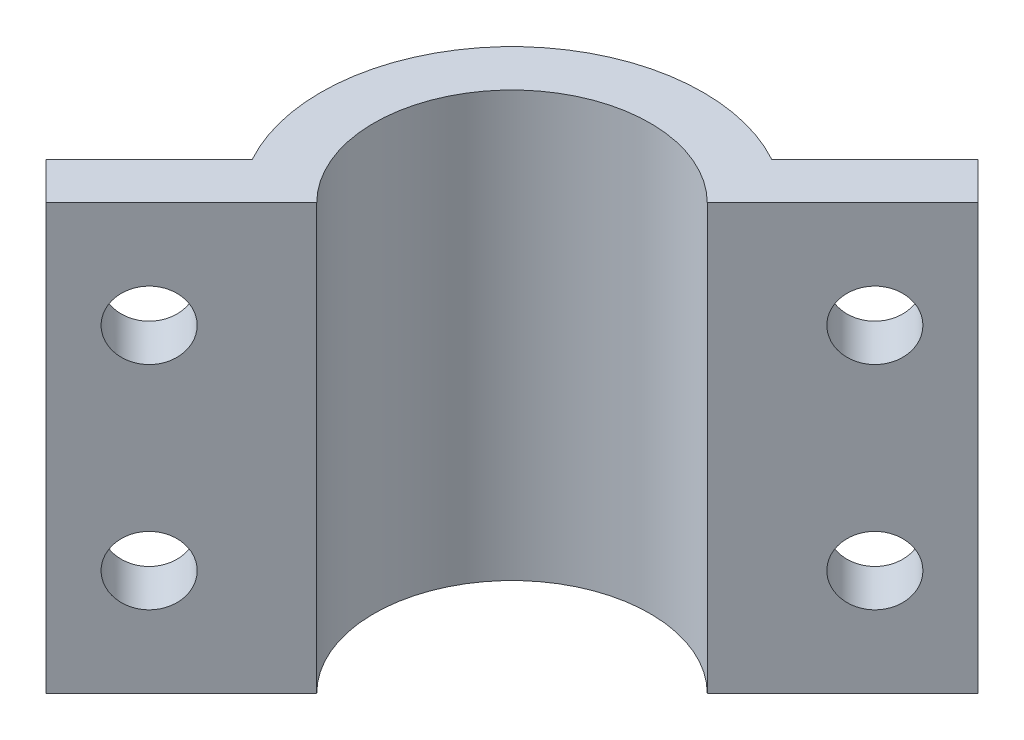
SolidWorks part; units mm, degrees
material "PLA"
ref_plane "Front Plane" through (0, 0, 0) normal (0, 0, 1) x (1, 0, 0)
ref_plane "Top Plane" through (0, 0, 0) normal (0, 1, 0) x (1, 0, 0)
ref_plane "Right Plane" through (0, 0, 0) normal (1, 0, 0) x (0, 0, -1)
sketch "Sketch1" plane through (0, 0, 0) normal (0, 1, 0) x (1, 0, 0)
  line L0 (0, 90) -> (0, -90) construction
  line L1 (-90, 0) -> (90, 0) construction
  line L2 (50, 10) -> (84, 10)
  line L3 (4, 90) -> (-4, 90)
  line L4 (10, 84) -> (10, 50)
  line L5 (4, -90) -> (-4, -90)
  line L6 (-10, 84) -> (-10, 50)
  line L7 (-84, 10) -> (-50, 10)
  line L8 (-90, 4) -> (-90, -4)
  line L9 (-84, -10) -> (-50, -10)
  line L10 (90, 4) -> (90, -4)
  line L11 (10, -50) -> (10, -84)
  line L12 (50, -10) -> (84, -10)
  line L13 (-10, -50) -> (-10, -84)
  arc A0 (4, 90) -> (10, 84) centre (4, 84) cw
  arc A1 (-4, 90) -> (-10, 84) centre (-4, 84) ccw
  arc A2 (84, 10) -> (90, 4) centre (84, 4) cw
  arc A3 (84, -10) -> (90, -4) centre (84, -4) ccw
  arc A4 (10, -84) -> (4, -90) centre (4, -84) cw
  arc A5 (-4, -90) -> (-10, -84) centre (-4, -84) cw
  arc A6 (-90, -4) -> (-84, -10) centre (-84, -4) ccw
  arc A7 (-84, 10) -> (-90, 4) centre (-84, 4) ccw
  arc A8 (50, 10) -> (10, 50) centre (50, 50) cw
  arc A9 (10, -50) -> (50, -10) centre (50, -50) cw
  arc A10 (-50, -10) -> (-10, -50) centre (-50, -50) cw
  arc A11 (-10, 50) -> (-50, 10) centre (-50, 50) cw
  point P5 (0, 0)
  point P8 (0, 0)
  point P16 (0, 90)
  point P23 (10, 90)
  point P26 (-10, 90)
  point P43 (10, -10)
  point P46 (-10, -10)
  dimension "D1" = 20
  dimension "D3" = 6
  dimension "D4" = 40
  dimension "D2" = 180
extrude "Boss-Extrude1" add sketch "Sketch1" along normal mid plane 3
hole_wizard "M3 Clearance Hole1" positions "Sketch3" profile "Sketch4" hole size "M3" standard "ANSI Metric" end condition up to next
sketch "Sketch3" plane through (0, 1.5, 0) normal (0, 1, 0) x (1, 0, 0)
  line L2 (-84, 4) -> (-39, 4) construction
  line L3 (-84, 4) -> (-84, -4) construction
  line L4 (-84, -4) -> (-39, -4) construction
  line L5 (-39, 4) -> (-39, -4) construction
  line L7 (-4, 84) -> (4, 84) construction
  line L8 (-4, 84) -> (-4, 39) construction
  line L9 (-4, 39) -> (4, 39) construction
  line L10 (4, 84) -> (4, 39) construction
  line L12 (39, 4) -> (84, 4) construction
  line L13 (39, 4) -> (39, -4) construction
  line L14 (39, -4) -> (84, -4) construction
  line L15 (84, 4) -> (84, -4) construction
  line L17 (-4, -39) -> (4, -39) construction
  line L18 (-4, -39) -> (-4, -84) construction
  line L19 (-4, -84) -> (4, -84) construction
  line L20 (4, -39) -> (4, -84) construction
  point P0 (-84, 4)
  point P3 (-84, -4)
  point P6 (-4, 84)
  point P9 (4, 84)
  point P12 (84, 4)
  point P15 (84, -4)
  point P18 (4, -84)
  point P21 (-4, -84)
  point P24 (-39, 4)
  point P26 (-39, -4)
  point P28 (39, 4)
  point P30 (39, -4)
  point P32 (4, -39)
  point P34 (-4, -39)
  point P36 (-4, 39)
  point P38 (4, 39)
  dimension "D1" = 45
sketch "Sketch4" plane through (-84, 1.5, -4) normal (1, 0, 0) x (0, 0, 1)
  line L0 (0, 0) -> (0, 3)
  line L1 (0, 3) -> (1.6, 3)
  line L2 (1.6, 3) -> (1.6, 0)
  line L5 (1.6, 0) -> (0, 0)
  line L11 (0, -6.35) -> (0, 107.95) construction
  dimension "Thru Hole Dia." = 3.2
  dimension "Thru Hole Depth" = 3
sketch "Sketch5" plane through (0, 1.5, 0) normal (0, 1, 0) x (1, 0, 0)
  circle A0 centre (0, 0) radius 15
  dimension "D1" = 30
extrude "Cut-Extrude1" cut sketch "Sketch5" against normal through all both and the other way through all
sketch "Sketch6" plane through (0, -1.5, 0) normal (0, -1, 0) x (1, 0, 0)
  line L0 (-21.7157, 21.7157) -> (21.7157, -21.7157) construction
  line L1 (-15.7626, 8.6915) -> (-25.4731, 18.402)
  line L2 (-25.4731, 18.402) -> (-18.402, 25.4731)
  line L3 (-18.402, 25.4731) -> (-8.6915, 15.7626)
  line L4 (8.6915, -15.7626) -> (18.402, -25.4731)
  line L5 (18.402, -25.4731) -> (25.4731, -18.402)
  line L6 (25.4731, -18.402) -> (15.7626, -8.6915)
  circle A0 centre (0, 0) radius 13
  arc A1 (-15.7626, 8.6915) -> (8.6915, -15.7626) centre (0, 0) ccw
  arc A2 (-50, 10) -> (-10, 50) centre (-50, 50) ccw construction
  arc A3 (50, -10) -> (10, -50) centre (50, -50) ccw construction
  circle A4 centre (0, 0) radius 18 construction
  arc A5 (15.7626, -8.6915) -> (-8.6915, 15.7626) centre (0, 0) ccw
  dimension "D1" = 26
  dimension "D3" = 5
  dimension "D4" = 5
  dimension "D2" = 5
extrude "Boss-Extrude2" add sketch "Sketch6" along normal blind 40 contours L1 L2 L3 A5 L6 L5 L4 A1 | A0
hole_wizard "M6 Clearance Hole1" positions "Sketch10" profile "Sketch8" hole size "M6" standard "ANSI Metric" end condition up to next
sketch "Sketch10" plane through (3.5355, 0, 3.5355) normal (0.7071, 0, 0.7071) x (0.7071, 0, -0.7071)
  line L0 (-24.158, -41.5) -> (-24.158, -1.5) construction
  line L1 (-31.0244, -41.5) -> (-17.2916, -41.5) construction
  line L2 (-52.3259, -1.5) -> (-28.2843, -1.5) construction
  line L4 (24.158, -41.5) -> (24.158, -1.5) construction
  line L5 (31.0244, -41.5) -> (17.2916, -41.5) construction
  line L6 (249.5584, -1.5) -> (31.0244, -1.5) construction
  line L9 (-24.158, -11.5) -> (24.158, -11.5)
  line L10 (-24.158, -11.5) -> (-24.158, -31.5)
  line L11 (-24.158, -31.5) -> (24.158, -31.5)
  line L12 (24.158, -11.5) -> (24.158, -31.5)
  line L13 (-17.2916, -1.5) -> (17.2916, -1.5) construction
  point P0 (-24.158, -11.5)
  point P2 (-24.158, -31.5)
  point P4 (24.158, -11.5)
  point P6 (24.158, -31.5)
  dimension "D1" = 20
  dimension "D2" = 10
sketch "Sketch8" plane through (-13.5468, -11.5, 20.6178) normal (0, 1, 0) x (0.7071, 0, -0.7071)
  line L0 (0, 0) -> (0, 10)
  line L1 (0, 10) -> (3.2, 10)
  line L2 (3.2, 10) -> (3.2, 0)
  line L5 (3.2, 0) -> (0, 0)
  line L11 (0, -6.35) -> (0, 107.95) construction
  dimension "Thru Hole Dia." = 6.4
  dimension "Thru Hole Depth" = 10
sketch "Sketch11" plane through (0, -41.5, 0) normal (0, -1, 0) x (1, 0, 0)
  line L0 (-21.9376, 21.9376) -> (21.9376, -21.9376)
  line L1 (18.402, -25.4731) -> (25.4731, -18.402) construction
  line L6 (8.6915, -15.7626) -> (18.402, -25.4731)
  line L7 (18.402, -25.4731) -> (25.4731, -18.402)
  line L8 (25.4731, -18.402) -> (15.7626, -8.6915)
  line L9 (-8.6915, 15.7626) -> (-18.402, 25.4731)
  line L10 (-18.402, 25.4731) -> (-25.4731, 18.402)
  line L11 (-25.4731, 18.402) -> (-15.7626, 8.6915)
  line L12 (8.6915, -15.7626) -> (18.402, -25.4731)
  line L13 (18.402, -25.4731) -> (21.9376, -21.9376)
  line L16 (-21.9376, 21.9376) -> (-25.4731, 18.402)
  line L17 (-25.4731, 18.402) -> (-15.7626, 8.6915)
  arc A2 (-15.7626, 8.6915) -> (8.6915, -15.7626) centre (0, 0) ccw
  arc A3 (15.7626, -8.6915) -> (-8.6915, 15.7626) centre (0, 0) ccw
  arc A4 (-15.7626, 8.6915) -> (8.6915, -15.7626) centre (0, 0) ccw
  dimension "D1" = 0
extrude "Cut-Extrude2" cut sketch "Sketch11" against normal up to surface (40 mm away) flip side to cut up to face at (4, -1.5, -40.6)
sketch "Sketch12" plane through (0, 0, 0) normal (1, 0, 0) x (0, 0, -1)
  line L1 (-93.0895, 3.6447) -> (90, 3.6447)
  line L2 (-93.0895, 3.6447) -> (-93.0895, -1.5)
  line L3 (-93.0895, -1.5) -> (90, -1.5)
  line L4 (90, 3.6447) -> (90, -1.5)
extrude "Cut-Extrude4" cut sketch "Sketch12" against normal through all both and the other way through all
equation "\"D4@Sketch6\"=\"D3@Sketch6\""
